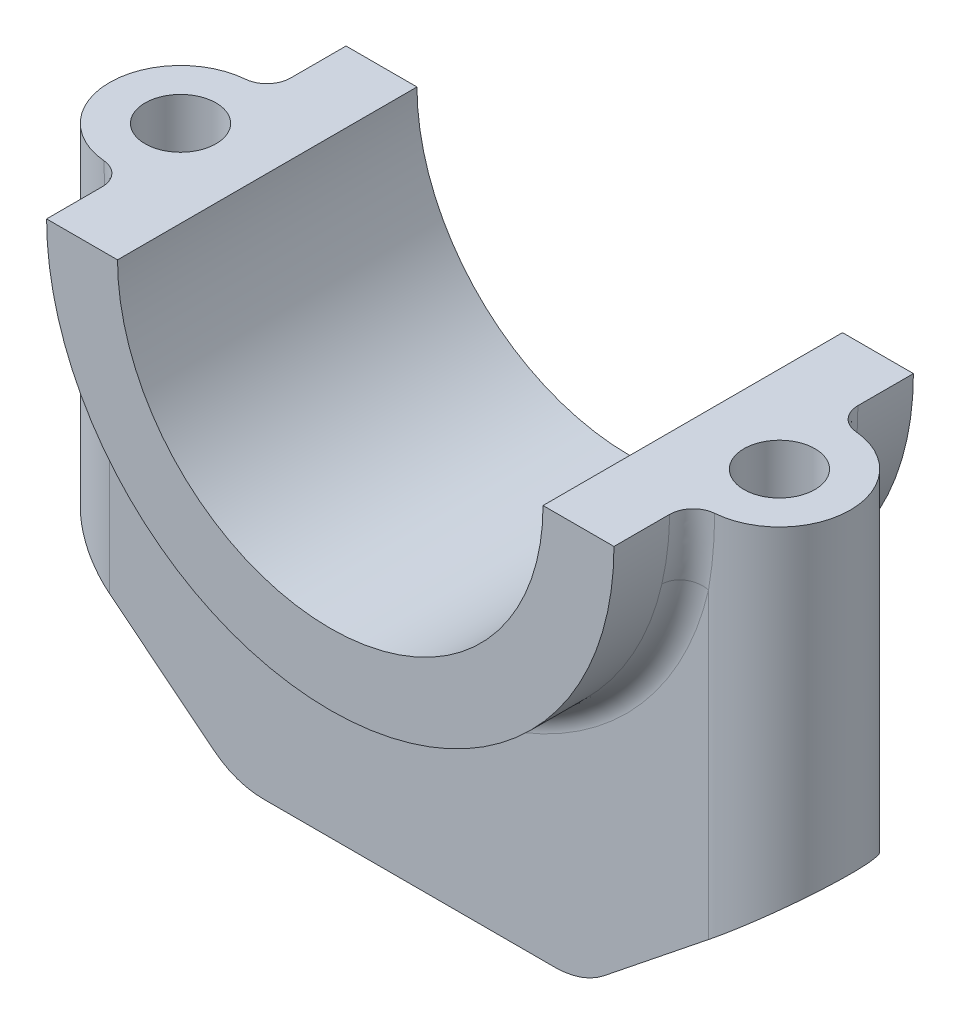
SolidWorks part; units mm, degrees
ref_plane "Front Plane" through (0, 0, 0) normal (0, 0, 1) x (1, 0, 0)
ref_plane "Top Plane" through (0, 0, 0) normal (0, 1, 0) x (1, 0, 0)
ref_plane "Right Plane" through (0, 0, 0) normal (1, 0, 0) x (0, 0, -1)
sketch "Sketch7" plane through (0, 0, 0) normal (0, 0, 1) x (1, 0, 0)
  line L0 (-36, 0) -> (36, 0)
  arc A0 (-36, 0) -> (36, 0) centre (0, 0) ccw
  arc A1 (-27, 0) -> (27, 0) centre (0, 0) ccw
  dimension "D1" = 54
  dimension "D2" = 72
extrude "Boss-Extrude3" add sketch "Sketch7" along normal mid plane 38 contours A1 L0 A0
ref_plane "Plane2" through (0, -60, 0) normal (0, 1, 0) x (1, 0, 0)
sketch "Sketch9" plane through (0, -60, 0) normal (0, 1, 0) x (1, 0, 0)
  line L0 (-38, 0) -> (38, 0) construction
  line L1 (-38, 9) -> (38, 9)
  line L2 (-38, -9) -> (38, -9)
  arc A0 (-38, 9) -> (-38, -9) centre (-38, 0) ccw
  arc A1 (38, -9) -> (38, 9) centre (38, 0) ccw
  point P2 (0, 0)
  dimension "D2" = 9
  dimension "D1" = 76
extrude "Boss-Extrude4" add sketch "Sketch9" along normal up to surface (60 mm away) up to face at (-31.5, 0, 0)
sketch "Sketch10" plane through (0, 0, 9) normal (0, 0, 1) x (1, 0, 0)
  line L1 (27, 0) -> (-27, 0)
  line L2 (27, 0) -> (-27, 0)
  arc A1 (-27, 0) -> (27, 0) centre (0, 0) ccw
  arc A2 (-27, 0) -> (27, 0) centre (0, 0) ccw
  dimension "D1" = 0
extrude "Cut-Extrude3" cut sketch "Sketch10" against normal up to next
sketch "Sketch11" plane through (0, 0, 0) normal (0, 1, 0) x (1, 0, 0)
  line L0 (0, -20.9) -> (0, 20.9) construction
  line L7 (36, 19) -> (27, 19)
  line L8 (27, 19) -> (27, -19)
  line L9 (27, -19) -> (36, -19)
  line L10 (36, -19) -> (36, -9)
  line L11 (36, -9) -> (38, -9)
  line L12 (38, 9) -> (36, 9)
  line L13 (36, 9) -> (36, 19)
  line L14 (36, 19) -> (27, 19)
  line L15 (27, 19) -> (27, -19)
  line L16 (27, -19) -> (36, -19)
  line L17 (36, -19) -> (36, -9)
  line L18 (36, -9) -> (38, -9)
  line L19 (38, 9) -> (36, 9)
  line L20 (36, 9) -> (36, 19)
  circle A0 centre (38, 0) radius 4.5
  arc A1 (38, -9) -> (38, 9) centre (38, 0) ccw
  arc A2 (38, -9) -> (38, 9) centre (38, 0) ccw
  circle A3 centre (-38, 0) radius 4.5
  dimension "D2" = 9
  dimension "D1" = 0
extrude "Cut-Extrude4" cut sketch "Sketch11" against normal up to next contours A0 | A3
ref_plane "Plane3" through (0, 0, 14) normal (0, 0, 1) x (1, 0, 0)
sketch "Sketch12" plane through (0, 0, 14) normal (0, 0, 1) x (1, 0, 0)
  line L0 (-47, -60) -> (-22, -60)
  line L1 (-22, -60) -> (-47, -40)
  line L2 (-47, 0) -> (-47, -60) construction
  line L3 (-47, -40) -> (-47, -60)
  line L5 (38, 0) -> (36, 0)
  line L6 (-36, 0) -> (-38, 0)
  line L7 (-38, 0) -> (-38, -60)
  line L8 (-38, -60) -> (38, -60)
  line L9 (38, -60) -> (38, 0)
  line L10 (38, 0) -> (36, 0)
  line L11 (-36, 0) -> (-38, 0)
  line L12 (-38, 0) -> (-38, -60)
  line L13 (-38, -60) -> (38, -60)
  line L14 (38, -60) -> (38, 0)
  arc A1 (-36, 0) -> (36, 0) centre (0, 0) ccw
  arc A2 (-36, 0) -> (36, 0) centre (0, 0) ccw
  dimension "D2" = 20
  dimension "D3" = 25
  dimension "D1" = 0
extrude "Cut-Extrude5" cut sketch "Sketch12" against normal up to surface (23 mm away) contours L12 L1 L3 L0 | L1 L12 L0 up to face at (0, -26, -9)
mirror "Mirror1" about plane through (0, 0, 0) normal (1, 0, 0) of "Cut-Extrude5"
fillet "Fillet2" radius 10 2 edges at (22, -60, 0) (-22, -60, 0)
fillet "Fillet3" radius 3 2 edges at (0, -36, -9) (0, -36, 9)
